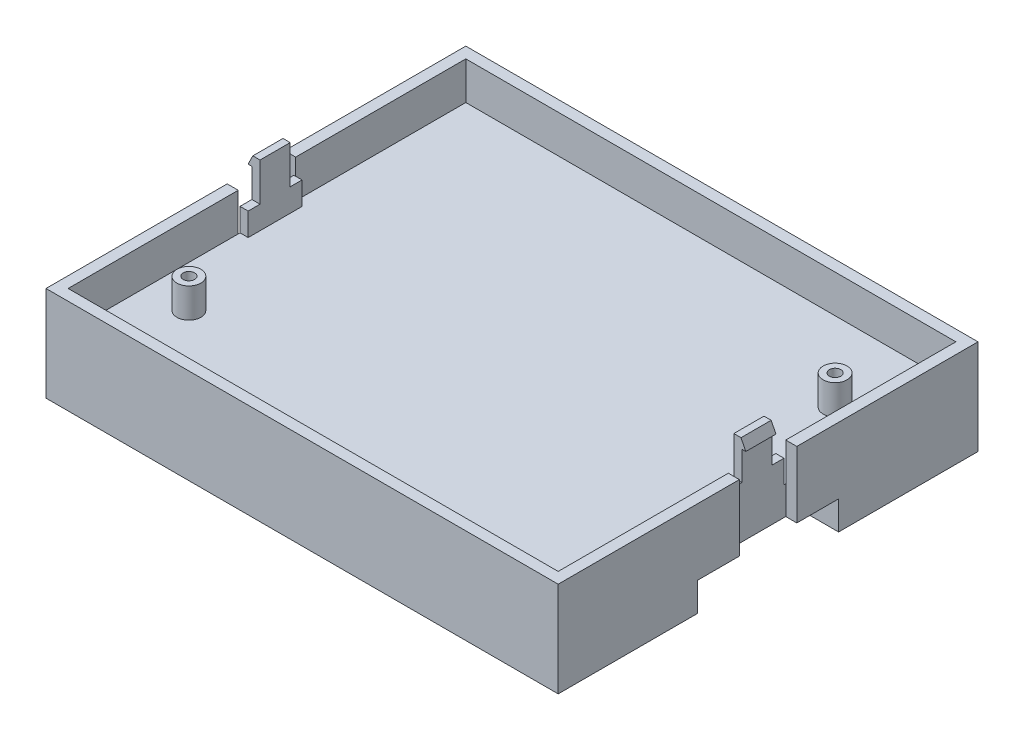
SolidWorks part; units mm, degrees
ref_plane "Alzado" through (0, 0, 0) normal (0, 0, 1) x (1, 0, 0)
ref_plane "Planta" through (0, 0, 0) normal (0, 1, 0) x (1, 0, 0)
ref_plane "Vista lateral" through (0, 0, 0) normal (1, 0, 0) x (0, 0, -1)
sketch "Sketch1" plane through (0, 0, 0) normal (0, 1, 0) x (1, 0, 0)
  line L1 (-53.5, -43.85) -> (53.5, -43.85)
  line L2 (-53.5, -43.85) -> (-53.5, 43.85)
  line L3 (-53.5, 43.85) -> (53.5, 43.85)
  line L4 (53.5, -43.85) -> (53.5, 43.85)
  line L5 (-53.5, -43.85) -> (53.5, 43.85) construction
  line L6 (-53.5, 43.85) -> (53.5, -43.85) construction
  point P0 (0, 0)
  dimension "D1" = 107
  dimension "D2" = 87.7
extrude "Boss-Extrude1" add sketch "Sketch1" along normal blind 13.85
sketch "Sketch2" plane through (0, 13.85, 0) normal (0, 1, 0) x (1, 0, 0)
  line L8 (51.19, -41.54) -> (51.19, 41.54)
  line L9 (51.19, 41.54) -> (-51.19, 41.54)
  line L10 (-51.19, 41.54) -> (-51.19, -41.54)
  line L11 (-51.19, -41.54) -> (51.19, -41.54)
  line L12 (51.19, -41.54) -> (51.19, 41.54)
  line L13 (51.19, 41.54) -> (-51.19, 41.54)
  line L14 (-51.19, 41.54) -> (-51.19, -41.54)
  line L15 (-51.19, -41.54) -> (51.19, -41.54)
  dimension "D1" = 2.31
extrude "Cut-Extrude1" cut sketch "Sketch2" against normal blind 7.9
sketch "Sketch4" plane through (0, 5.95, 0) normal (0, 1, 0) x (1, 0, 0)
  circle A0 centre (42.5, 25) radius 1.2
  circle A1 centre (-42.5, -25) radius 1.2
  circle A2 centre (-42.5, -25) radius 2.5
  circle A3 centre (42.5, 25) radius 2.5
  dimension "D1" = 2.4
  dimension "D6" = 5
  dimension "D2" = 25
  dimension "D3" = 25
  dimension "D4" = 42.5
  dimension "D5" = 42.5
extrude "Boss-Extrude2" add sketch "Sketch4" along normal blind 6.2
sketch "Sketch7" plane through (-51.19, 0, 0) normal (1, 0, 0) x (0, 0, -1)
  line L0 (41.54, 5.95) -> (-41.54, 5.95) construction
  line L1 (-5.625, 5.95) -> (5.625, 5.95)
  line L2 (-5.625, 5.95) -> (-5.625, 10.75)
  line L3 (-5.625, 10.75) -> (5.625, 10.75)
  line L4 (5.625, 5.95) -> (5.625, 10.75)
  point P6 (0, 5.95)
  dimension "D1" = 11.25
  dimension "D2" = 4.8
extrude "Boss-Extrude3" add sketch "Sketch7" along normal blind 1.7
sketch "Sketch8" plane through (0, 0, 0) normal (0, 0, 1) x (1, 0, 0)
  line L0 (-49.49, 10.75) -> (-49.49, 18.75)
  line L1 (-49.49, 18.75) -> (-50.99, 18.75)
  line L2 (-50.99, 18.75) -> (-51.99, 16.75)
  line L3 (-51.99, 16.75) -> (-51.19, 16.75)
  line L4 (-51.19, 16.75) -> (-51.19, 10.75)
  line L5 (-51.19, 10.75) -> (-49.49, 10.75)
  line L6 (51.19, 5.95) -> (-51.19, 5.95) construction
  dimension "D1" = 12.8
  dimension "D2" = 2.5
  dimension "D3" = 2
  dimension "D4" = 1.5
extrude "Boss-Extrude4" add sketch "Sketch8" along normal mid plane 6.3
mirror "Mirror1" about plane through (0, 0, 0) normal (1, 0, 0) of "Boss-Extrude4"
mirror "Mirror2" about plane through (0, 0, 0) normal (1, 0, 0) of "Boss-Extrude3"
sketch "Sketch22" plane through (0, 5.95, 0) normal (0, 1, 0) x (1, 0, 0)
  line L5 (-53.5, 43.85) -> (-53.5, -43.85) construction
  line L6 (-51.19, 0) -> (-51.19, -6)
  line L7 (-51.19, 0) -> (-51.19, 6)
  line L8 (-51.19, 6) -> (-53.5, 6)
  line L9 (-53.5, 6) -> (-53.5, -6)
  line L10 (-53.5, -6) -> (-51.19, -6)
extrude "Cut-Extrude8" cut sketch "Sketch22" against normal blind 12 and the other way blind 8
mirror "Mirror3" about plane through (0, 0, 0) normal (1, 0, 0) of "Cut-Extrude8"
sketch "Sketch23" plane through (0, 0, 0) normal (0, -1, 0) x (-1, 0, 0)
  line L0 (53.5, -43.85) -> (-53.5, -43.85)
  line L1 (-53.5, -43.85) -> (-53.5, -14.7317)
  line L2 (-53.5, -43.85) -> (-53.5, -6) construction
  line L3 (-53.5, -14.7317) -> (-37.0567, -14.7317)
  line L4 (-37.0567, -14.7317) -> (-37.0567, -6)
  line L5 (-37.0567, -6) -> (37.0567, -6)
  line L6 (37.0567, -6) -> (37.0567, -14.7317)
  line L7 (37.0567, -14.7317) -> (53.5, -14.7317)
  line L8 (53.5, -6) -> (53.5, -43.85) construction
  line L9 (53.5, -14.7317) -> (53.5, -43.85)
extrude "Boss-Extrude7" add sketch "Sketch23" along normal blind 6
sketch "Sketch24" plane through (37.0567, 0, 0) normal (1, 0, 0) x (0, 0, -1)
  line L0 (-6, 0) -> (-14.7317, 0)
  line L11 (-6, 0) -> (-6, -3)
  line L12 (-6, -6) -> (-6, 0) construction
  line L13 (-6, -3) -> (-14.7317, -3)
  line L14 (-14.7317, -6) -> (-14.7317, 0) construction
  line L15 (-14.7317, -3) -> (-14.7317, 0)
extrude "Cut-Extrude10" cut sketch "Sketch24" against normal through all
chamfer "Chamfer1" distance 1.5 angle 45 1 edges at (0, -3, 6)
mirror "Mirror4" about plane through (0, 0, 0) normal (0, 0, 1) of "Boss-Extrude7"
mirror "Mirror7" about plane through (0, 0, 0) normal (0, 0, 1) of "Cut-Extrude10"
chamfer "Chamfer2" distance 1.5 angle 45 1 edges at (0, -3, -6)
